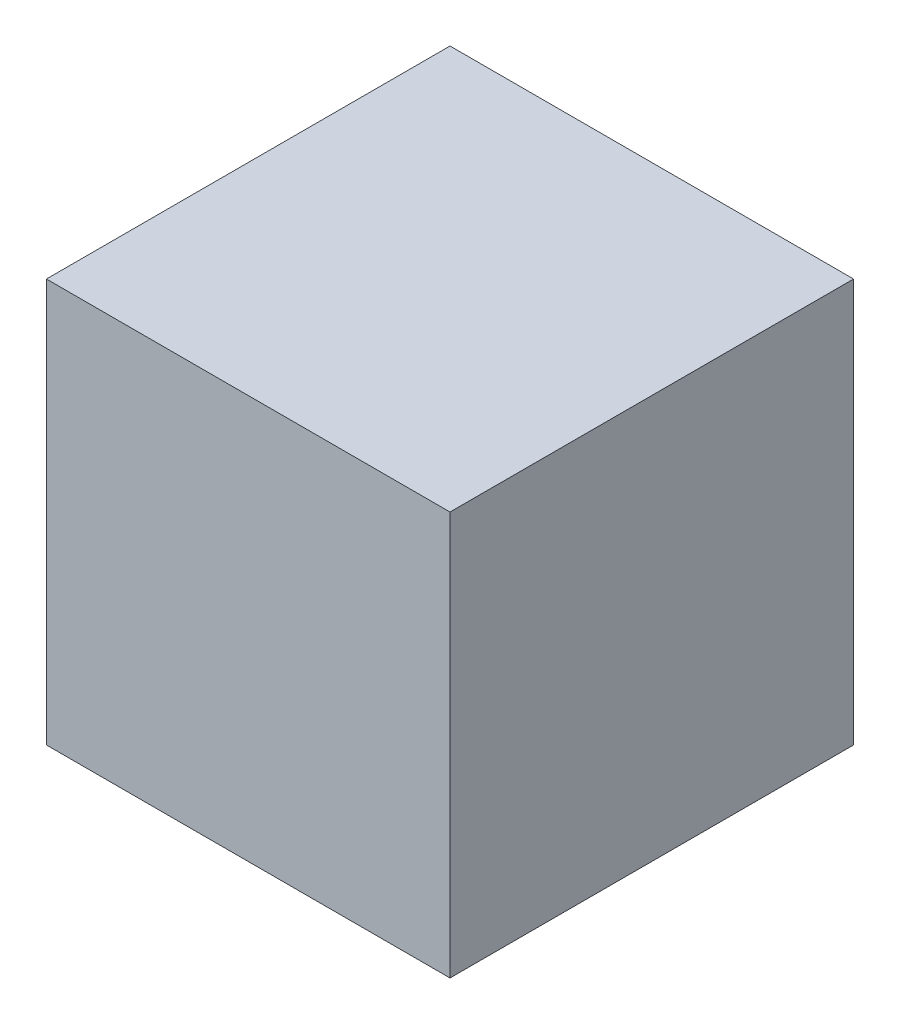
SolidWorks part; units mm, degrees
ref_plane "Front Plane" through (0, 0, 0) normal (0, 0, 1) x (1, 0, 0)
ref_plane "Top Plane" through (0, 0, 0) normal (0, 1, 0) x (1, 0, 0)
ref_plane "Right Plane" through (0, 0, 0) normal (1, 0, 0) x (0, 0, -1)
sketch "Sketch1" plane through (0, 0, 0) normal (0, 1, 0) x (1, 0, 0)
  line L1 (-180.7779, 161.4761) -> (92.2721, 161.4761)
  line L2 (-180.7779, 161.4761) -> (-180.7779, -111.5739)
  line L3 (-180.7779, -111.5739) -> (92.2721, -111.5739)
  line L4 (92.2721, 161.4761) -> (92.2721, -111.5739)
  dimension "D1" = 273.05
  dimension "D2" = 273.05
extrude "Boss-Extrude1" add sketch "Sketch1" along normal blind 273.05
